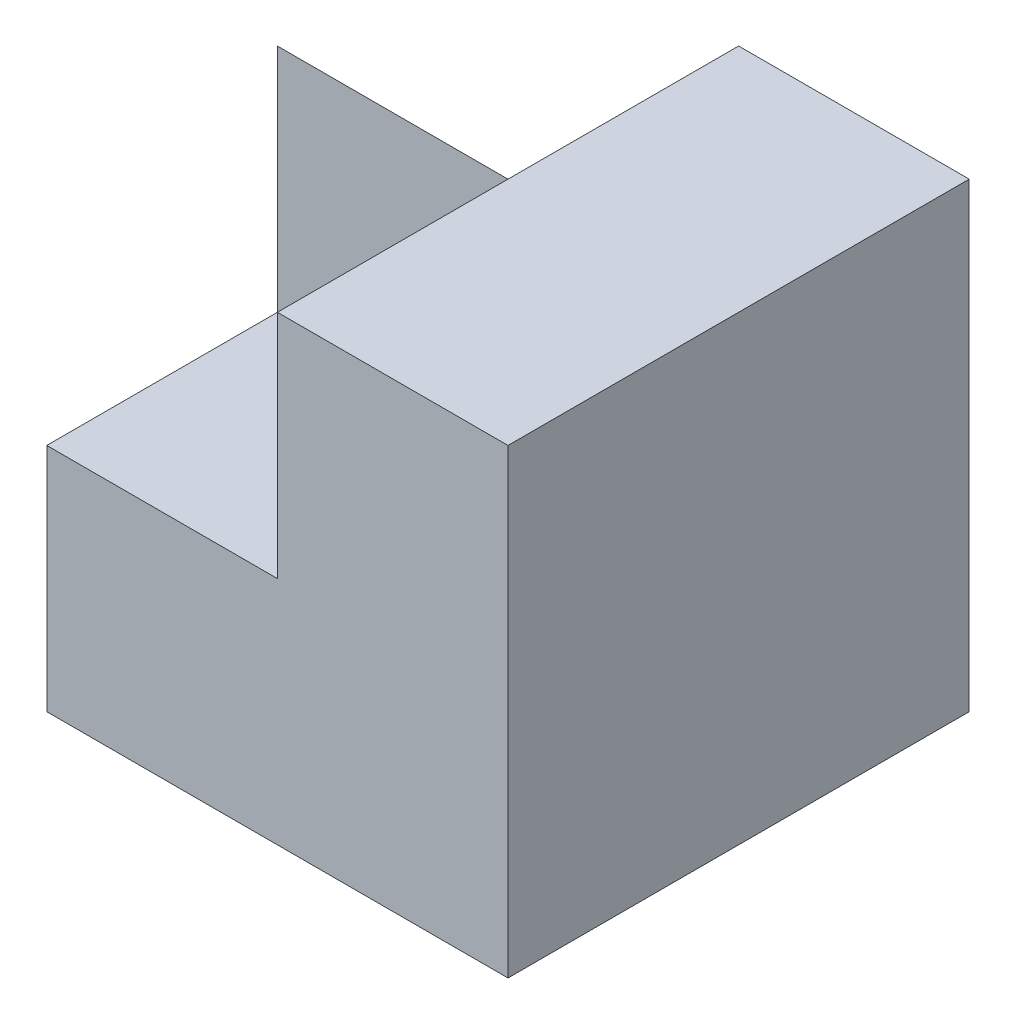
SolidWorks part; units mm, degrees
ref_plane "Front" through (0, 0, 0) normal (0, 0, 1) x (1, 0, 0)
ref_plane "Top" through (0, 0, 0) normal (0, 1, 0) x (1, 0, 0)
ref_plane "Right" through (0, 0, 0) normal (1, 0, 0) x (0, 0, -1)
sketch "Sketch1" plane through (0, 0, 0) normal (0, 1, 0) x (1, 0, 0)
  line L1 (-2, -2) -> (2, -2)
  line L2 (-2, -2) -> (-2, 2)
  line L3 (-2, 2) -> (2, 2)
  line L4 (2, -2) -> (2, 2)
  line L5 (-2, -2) -> (2, 2) construction
  line L6 (-2, 2) -> (2, -2) construction
  point P0 (0, 0)
  dimension "D1" = 4
  dimension "D2" = 4
extrude "Boss-Extrude1" add sketch "Sketch1" along normal blind 4
sketch "Sketch2" plane through (-2, 0, 0) normal (-1, 0, 0) x (0, 0, 1)
  line L0 (-2, 2) -> (0, 4)
  line L3 (0, 4) -> (0, 2)
  line L5 (0, 2) -> (2, 2)
  line L9 (-2, 0) -> (2, 0)
  line L10 (2, 0) -> (2, 4)
  line L11 (2, 4) -> (-2, 4)
  line L12 (-2, 4) -> (-2, 0)
  line L13 (-2, 0) -> (2, 0)
  line L14 (2, 0) -> (2, 4)
  line L15 (2, 4) -> (-2, 4)
  line L16 (-2, 4) -> (-2, 0)
  dimension "D1" = 0
extrude "Cut-Extrude1" cut sketch "Sketch2" against normal blind 2
